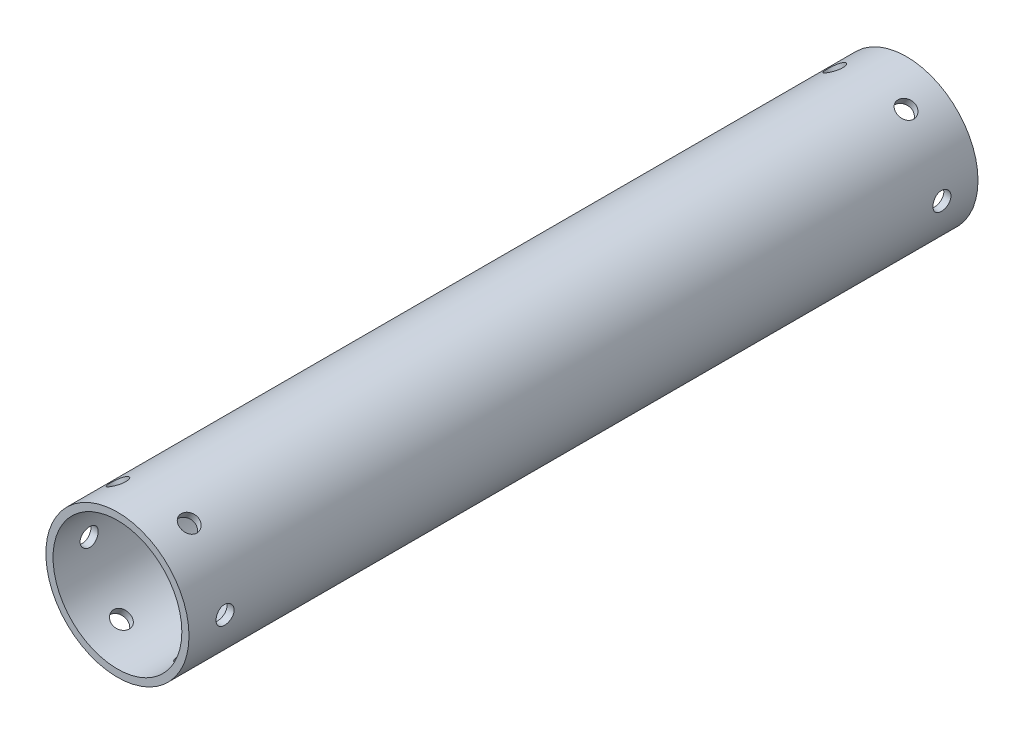
SolidWorks part; units mm, degrees
material "6063-T5"
ref_plane "Plano frontal" through (0, 0, 0) normal (0, 0, 1) x (1, 0, 0)
ref_plane "Plano superior" through (0, 0, 0) normal (0, 1, 0) x (1, 0, 0)
ref_plane "Plano direito" through (0, 0, 0) normal (1, 0, 0) x (0, 0, -1)
sketch "Esboço1" plane through (0, 0, 0) normal (0, 0, 1) x (1, 0, 0)
  line L0 (0, 0) -> (-50000, 0) construction
  line L1 (0, -1000) -> (0, 49000) construction
  circle A0 centre (0, 0) radius 31.75
  circle A1 centre (0, 0) radius 28.575
  dimension "D1" = 63.5
  dimension "D2" = 3.175
extrude "Ressalto-extrusão1" add sketch "Esboço1" along normal blind 350 contours A1 | A0
sketch "Esboço3" plane through (0, 0, 0) normal (1, 0, 0) x (0, 0, -1)
  line L0 (-1000, 0) -> (49000, 0) construction
  line L3 (-350, 28.575) -> (-350, -28.575) construction
  circle A0 centre (-16, 0) radius 4
  circle A1 centre (-334, 0) radius 4
  dimension "D1" = 8
  dimension "D3" = 8
  dimension "D2" = 12
  dimension "D4" = 12
extrude "Corte-extrusão1" cut sketch "Esboço3" against normal blind 45
pattern_circular "PadrãoCircular1" count 6 over 360 about axis through (0, 0, 350) along (0, 0, -1) of "Corte-extrusão1"
equation "\"D1@Esboço1\"=25.4*(2.5)"
equation "\"D2@Esboço1\"=25.4*(1/8)"
equation "\"D1@Esboço3\"=8"
equation "\"D2@Esboço3\"=1.5*\"D1@Esboço3\""
equation "\"D4@Esboço3\"=1.5*\"D3@Esboço3\""
